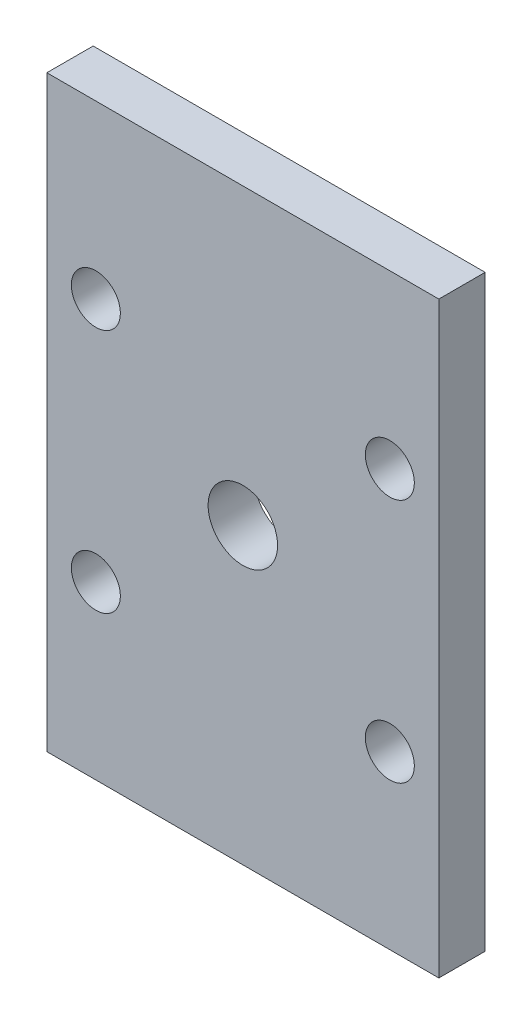
SolidWorks part; units mm, degrees
ref_plane "Front Plane" through (0, 0, 0) normal (0, 0, 1) x (1, 0, 0)
ref_plane "Top Plane" through (0, 0, 0) normal (0, 1, 0) x (1, 0, 0)
ref_plane "Right Plane" through (0, 0, 0) normal (1, 0, 0) x (0, 0, -1)
sketch "Sketch1" plane through (0, 0, 0) normal (0, 0, 1) x (1, 0, 0)
  line L1 (0, 0) -> (50.8, 0)
  line L2 (0, 0) -> (0, 76.2)
  line L3 (0, 76.2) -> (50.8, 76.2)
  line L4 (50.8, 0) -> (50.8, 76.2)
  dimension "D1" = 50.8
  dimension "D2" = 76.2
extrude "Boss-Extrude1" add sketch "Sketch1" along normal blind 6
hole_wizard "1/4 (0.25) Diameter Hole1" positions "Sketch3" profile "Sketch4" hole size "1/4" standard "ANSI Inch" end condition through all
sketch "Sketch3" plane through (0, 0, 6) normal (0, 0, 1) x (1, 0, 0)
  line L0 (50.8, 0) -> (50.8, 76.2) construction
  line L2 (0, 38.1) -> (50.8, 38.1) construction
  line L3 (0, 76.2) -> (0, 0) construction
  point P0 (44.45, 53.975)
  point P2 (6.35, 53.975)
  point P4 (6.35, 22.225)
  point P6 (44.45, 22.225)
  dimension "D1" = 38.1
  dimension "D2" = 6.35
  dimension "D3" = 31.75
  dimension "D4" = 15.875
sketch "Sketch4" plane through (44.45, 53.975, 6) normal (1, 0, 0) x (0, -1, 0)
  line L0 (0, 0) -> (0, 6)
  line L1 (0, 6) -> (3.175, 6)
  line L2 (3.175, 6) -> (3.175, 0)
  line L5 (3.175, 0) -> (0, 0)
  line L11 (0, -6.35) -> (0, 107.95) construction
  dimension "Thru Hole Dia." = 6.35
  dimension "Thru Hole Depth" = 6
sketch "Sketch5" plane through (0, 0, 6) normal (0, 0, 1) x (1, 0, 0)
  line L0 (0, 0) -> (50.8, 0) construction
  line L1 (50.8, 0) -> (50.8, 76.2) construction
  circle A0 centre (25.4, 38.1) radius 4.5
  dimension "D1" = 9
  dimension "D2" = 38.1
  dimension "D3" = 25.4
extrude "Cut-Extrude1" cut sketch "Sketch5" against normal through all
